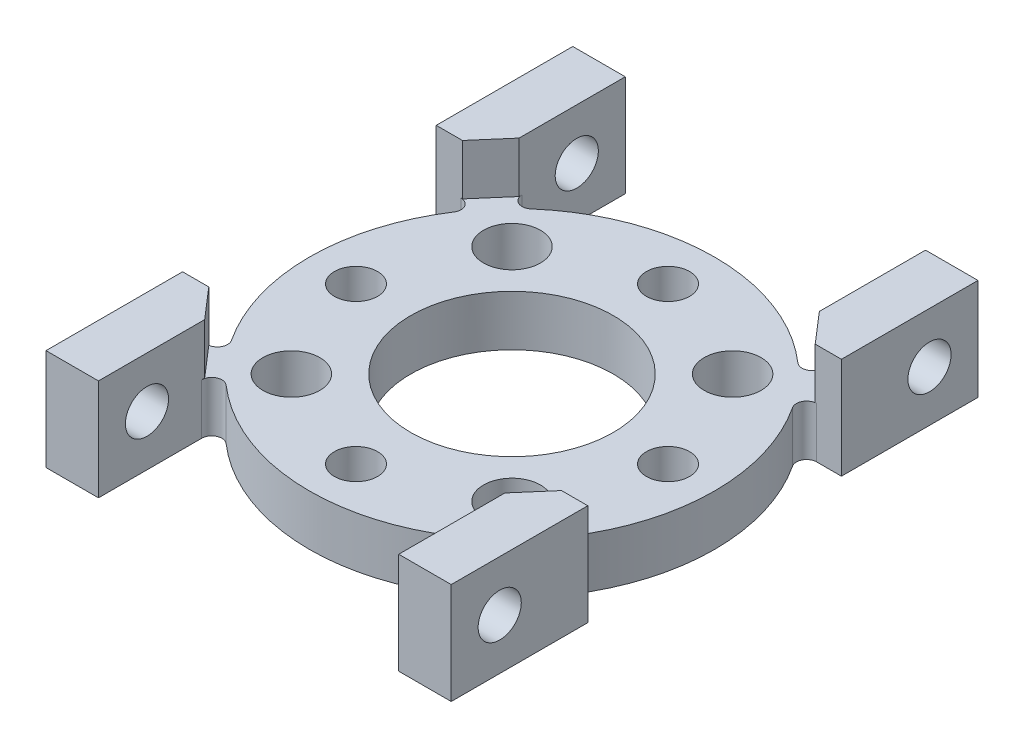
SolidWorks part; units mm, degrees
material "6061 Alloy"
ref_plane "Front Plane" through (0, 0, 0) normal (0, 0, 1) x (1, 0, 0)
ref_plane "Top Plane" through (0, 0, 0) normal (0, 1, 0) x (1, 0, 0)
ref_plane "Right Plane" through (0, 0, 0) normal (1, 0, 0) x (0, 0, -1)
sketch "Sketch1" plane through (0, 0, 0) normal (0, 1, 0) x (1, 0, 0)
  line L1 (-12.7, -16.51) -> (12.7, -16.51)
  line L2 (-12.7, -16.51) -> (-12.7, 16.51)
  line L3 (-12.7, 16.51) -> (12.7, 16.51)
  line L4 (12.7, -16.51) -> (12.7, 16.51)
  line L5 (-12.7, -16.51) -> (12.7, 16.51) construction
  line L6 (-12.7, 16.51) -> (12.7, -16.51) construction
  point P0 (0, 0)
  dimension "D1" = 25.4
  dimension "D2" = 33.02
extrude "Boss-Extrude1" add sketch "Sketch1" along normal blind 6.35
sketch "Sketch2" plane through (0, 0, 16.51) normal (0, 0, 1) x (1, 0, 0)
  line L0 (0, 6.35) -> (0, 0) construction
  line L1 (-12.7, 6.35) -> (12.7, 6.35) construction
  line L3 (-9.4107, 3.175) -> (9.4107, 3.175)
  line L4 (-9.4107, 3.175) -> (-9.4107, 6.35)
  line L5 (-9.4107, 6.35) -> (9.4107, 6.35)
  line L6 (9.4107, 3.175) -> (9.4107, 6.35)
  line L7 (-9.4107, 3.175) -> (9.4107, 6.35) construction
  line L8 (-9.4107, 6.35) -> (9.4107, 3.175) construction
  point P5 (0, 4.7625)
  dimension "D1" = 18.8214
  dimension "D2" = 3.175
extrude "Cut-Extrude1" cut sketch "Sketch2" against normal up to next
sketch "Sketch3" plane through (12.7, 0, 0) normal (1, 0, 0) x (0, 0, -1)
  line L0 (0, 0) -> (0, 6.35) construction
  line L1 (-16.51, 6.35) -> (16.51, 6.35) construction
  line L3 (-7.9502, 3.175) -> (7.9502, 3.175)
  line L4 (-7.9502, 3.175) -> (-7.9502, 6.35)
  line L5 (-7.9502, 6.35) -> (7.9502, 6.35)
  line L6 (7.9502, 3.175) -> (7.9502, 6.35)
  line L7 (-7.9502, 3.175) -> (7.9502, 6.35) construction
  line L8 (-7.9502, 6.35) -> (7.9502, 3.175) construction
  point P5 (0, 4.7625)
  dimension "D1" = 15.9004
  dimension "D2" = 3.175
extrude "Cut-Extrude2" cut sketch "Sketch3" against normal through all
sketch "Sketch4" plane through (0, 3.175, 0) normal (0, 1, 0) x (1, 0, 0)
  circle A0 centre (0, 0) radius 6.35
extrude "Cut-Extrude3" cut sketch "Sketch4" against normal up to next
sketch "Sketch5" plane through (0, 3.175, 0) normal (0, 1, 0) x (-1, 0, 0)
  line L0 (12.7, -7.9502) -> (11.1494, -7.9502)
  line L1 (12.7, -7.9502) -> (9.4107, -7.9502) construction
  line L2 (12.7, 7.9502) -> (9.4107, 7.9502) construction
  line L3 (11.1494, 7.9502) -> (12.7, 7.9502)
  line L4 (12.7, 7.9502) -> (12.7, 0)
  line L5 (12.7, 0) -> (12.7, -7.9502)
  line L6 (0, -16.51) -> (0, 16.51) construction
  line L7 (-9.4107, -16.51) -> (9.4107, -16.51) construction
  line L8 (9.4107, 16.51) -> (-9.4107, 16.51) construction
  line L9 (-12.7, 0) -> (-12.7, -7.9502)
  line L10 (-12.7, 7.9502) -> (-12.7, 0)
  line L11 (-11.1494, 7.9502) -> (-12.7, 7.9502)
  line L12 (-12.7, -7.9502) -> (-11.1494, -7.9502)
  arc A0 (10.6185, -6.9669) -> (10.6185, 6.9669) centre (0, 0) ccw
  arc A1 (10.6185, 6.9669) -> (11.1494, 7.9502) centre (11.1494, 7.3152) cw
  arc A2 (11.1494, -7.9502) -> (10.6185, -6.9669) centre (11.1494, -7.3152) cw
  arc A3 (-11.1494, -7.9502) -> (-10.6185, -6.9669) centre (-11.1494, -7.3152) ccw
  arc A4 (-10.6185, 6.9669) -> (-11.1494, 7.9502) centre (-11.1494, 7.3152) ccw
  arc A5 (-10.6185, -6.9669) -> (-10.6185, 6.9669) centre (0, 0) cw
  point P16 (9.9038, 7.9502)
  point P19 (9.9038, -7.9502)
  point P35 (-9.9038, -7.9502)
  point P36 (-9.9038, 7.9502)
  line M3 (-9.4107, 7.9502) -> (-12.7, 7.9502)
  line M4 (-12.7, 7.9502) -> (-12.7, -7.9502)
  line M5 (-12.7, -7.9502) -> (-9.4107, -7.9502)
  line M9 (9.4107, -7.9502) -> (12.7, -7.9502)
  line M10 (12.7, -7.9502) -> (12.7, 7.9502)
  line M11 (12.7, 7.9502) -> (9.4107, 7.9502)
  dimension "D1" = 0.635
extrude "Cut-Extrude4" cut sketch "Sketch5" against normal up to next contours A2 A0 M9 M10 | A1 A0 M10 M11 | A3 A5 M4 M5 | A5 A4 M4 M3
sketch "Sketch6" plane through (0, 3.175, 0) normal (0, 1, 0) x (1, 0, 0)
  line L0 (-9.4107, -7.9502) -> (-9.4107, -16.51) construction
  line L1 (9.4107, -7.9502) -> (9.4107, -16.51) construction
  line L2 (-9.4107, -10.0404) -> (-9.4107, -16.51)
  line L3 (-9.4107, -16.51) -> (9.4107, -16.51)
  line L4 (9.4107, -16.51) -> (9.4107, -10.0404)
  line L5 (-12.7, 0) -> (12.7, 0) construction
  line L6 (9.4107, 16.51) -> (9.4107, 10.0404)
  line L7 (-9.4107, 16.51) -> (9.4107, 16.51)
  line L8 (-9.4107, 10.0404) -> (-9.4107, 16.51)
  arc A0 (-8.3578, -9.5623) -> (8.3578, -9.5623) centre (0, 0) ccw
  arc A1 (-10.6185, 6.9669) -> (-10.6185, -6.9669) centre (0, 0) ccw construction
  arc A2 (10.6185, -6.9669) -> (10.6185, 6.9669) centre (0, 0) ccw construction
  arc A3 (8.3578, -9.5623) -> (9.4107, -10.0404) centre (8.7757, -10.0404) cw
  arc A4 (-8.3578, -9.5623) -> (-9.4107, -10.0404) centre (-8.7757, -10.0404) ccw
  arc A5 (-8.3578, 9.5623) -> (-9.4107, 10.0404) centre (-8.7757, 10.0404) cw
  arc A6 (8.3578, 9.5623) -> (9.4107, 10.0404) centre (8.7757, 10.0404) ccw
  arc A7 (-8.3578, 9.5623) -> (8.3578, 9.5623) centre (0, 0) cw
  point P22 (9.4107, -8.5281)
  point P25 (-9.4107, -8.5281)
  point P34 (-9.4107, 8.5281)
  point P35 (9.4107, 8.5281)
  dimension "D1" = 0.635
extrude "Cut-Extrude5" cut sketch "Sketch6" against normal up to next
sketch "Sketch7" plane through (0, 6.35, 0) normal (0, 1, 0) x (1, 0, 0)
  line L0 (-11.0554, 7.9502) -> (-9.4107, 9.8552)
  line L2 (-9.4107, 9.8552) -> (-9.4107, 7.9502)
  line L3 (-9.4107, 7.9502) -> (-11.0554, 7.9502)
  line L4 (-11.0554, -7.9502) -> (-9.4107, -9.8552)
  line L5 (-12.7, -7.9502) -> (-9.4107, -7.9502) construction
  line L6 (-9.4107, -9.8552) -> (-9.4107, -7.9502)
  line L7 (-9.4107, -7.9502) -> (-11.0554, -7.9502)
  line L8 (9.4107, -9.8552) -> (11.0553, -7.9502)
  line L9 (9.4107, -7.9502) -> (12.7, -7.9502) construction
  line L10 (11.0553, -7.9502) -> (9.4107, -7.9502)
  line L11 (9.4107, -7.9502) -> (9.4107, -9.8552)
  line L12 (9.4107, 9.8552) -> (11.0553, 7.9502)
  line L13 (11.0553, 7.9502) -> (9.4107, 7.9502)
  line L14 (9.4107, 10.0404) -> (9.4107, 7.9502) construction
  line L15 (9.4107, 7.9502) -> (11.1494, 7.9502) construction
  line L16 (9.4107, 7.9502) -> (9.4107, 9.8552)
  line L21 (-12.7, 7.9502) -> (-9.4107, 7.9502) construction
  line L22 (9.4107, 7.9502) -> (12.7, 7.9502) construction
  dimension "D1" = 1.905
extrude "Cut-Extrude6" cut sketch "Sketch7" against normal blind 3.175
hole_wizard "#6-32 Tapped Hole1" positions "Sketch11" profile "Sketch10" tap size "#6-32" standard "Ansi Inch" end condition up to next
sketch "Sketch11" plane through (0, 3.175, 0) normal (0, 1, 0) x (-1, 0, 0)
  point P0 (0, -9.779)
  point P8 (-9.779, 0)
  point P9 (0, 9.779)
  point P10 (9.779, 0)
  dimension "D1" = 9.779
  dimension "D2" = 4
cosmetic thread "Hole Thread1" parameters "D2"=3.5052
cosmetic thread "Hole Thread2" parameters "D2"=3.5052
cosmetic thread "Hole Thread3" parameters "D2"=3.5052
cosmetic thread "Hole Thread4" parameters "D2"=3.5052
sketch "Sketch10" plane through (0, 3.175, -9.779) normal (1, 0, 0) x (0, 0, 1)
  line L0 (0, 0) -> (0, 3.175)
  line L1 (0, 3.175) -> (1.3525, 3.175)
  line L2 (1.3525, 3.175) -> (1.3525, 0)
  line L5 (1.3525, 0) -> (0, 0)
  line L11 (0, -6.35) -> (0, 107.95) construction
  dimension "Thru Tap Drill Dia." = 2.7051
  dimension "Thru Tap Drill Depth" = 3.175
hole_wizard "#28 (0.1405) Diameter Hole1" positions "Sketch13" profile "Sketch12" hole size "#28" standard "Ansi Inch" end condition up to next
sketch "Sketch13" plane through (0, 3.175, 0) normal (0, 1, 0) x (-1, 0, 0)
  line L0 (0, 0) -> (6.9148, -6.9148) construction
  point P0 (6.9148, -6.9148)
  point P16 (-6.9148, -6.9148)
  point P17 (-6.9148, 6.9148)
  point P18 (6.9148, 6.9148)
  dimension "D1" = 9.779
  dimension "D2" = 4
sketch "Sketch12" plane through (-6.9148, 3.175, -6.9148) normal (1, 0, 0) x (0, 0, 1)
  line L0 (0, 0) -> (0, 3.175)
  line L1 (0, 3.175) -> (1.7843, 3.175)
  line L2 (1.7843, 3.175) -> (1.7843, 0)
  line L5 (1.7843, 0) -> (0, 0)
  line L11 (0, -6.35) -> (0, 107.95) construction
  dimension "Thru Hole Dia." = 3.5687
  dimension "Thru Hole Depth" = 3.175
hole_wizard "#6-32 Tapped Hole2" positions "Sketch15" profile "Sketch14" tap size "#6-32" standard "Ansi Inch"
sketch "Sketch15" plane through (12.7, 0, 0) normal (1, 0, 0) x (0, 0, -1)
  line L0 (-16.51, 0) -> (-7.9502, 0) construction
  line L1 (-13.4704, 3.175) -> (0, 16.6454) construction
  line L2 (0, 16.6454) -> (13.4704, 3.175) construction
  line L3 (13.4704, 3.175) -> (-13.4704, 3.175) construction
  point P0 (-13.4704, 3.175)
  point P1 (13.4704, 3.175)
  dimension "D1" = 3.175
  dimension "D2" = 19.05
  dimension "D3" = 90
  dimension "D4" = 19.05
cosmetic thread "Hole Thread5" parameters "D2"=3.5052
cosmetic thread "Hole Thread6" parameters "D2"=3.5052
sketch "Sketch14" plane through (12.7, 3.175, 13.4704) normal (0, 1, 0) x (0, 0, -1)
  line L0 (0, 0) -> (0, 25.4)
  line L1 (0, 25.4) -> (1.3525, 25.4)
  line L2 (1.3525, 25.4) -> (1.3525, 0)
  line L5 (1.3525, 0) -> (0, 0)
  line L11 (0, -6.35) -> (0, 107.95) construction
  dimension "Thru Tap Drill Dia." = 2.7051
  dimension "Thru Tap Drill Depth" = 25.4
mirror "Mirror1" about plane through (0, 0, 0) normal (1, 0, 0) of "#6-32 Tapped Hole2"
